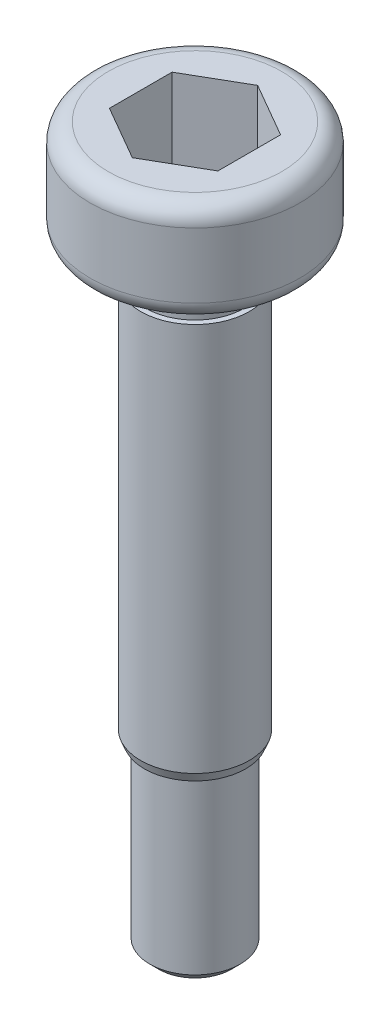
SolidWorks part; units mm, degrees
ref_plane "前视基准面" through (0, 0, 0) normal (0, 0, 1) x (1, 0, 0)
ref_plane "上视基准面" through (0, 0, 0) normal (0, 1, 0) x (1, 0, 0)
ref_plane "右视基准面" through (0, 0, 0) normal (1, 0, 0) x (0, 0, -1)
ref_plane "基准面1" through (0, 0, 0) normal (0, 0, -1) x (-1, 0, 0)
sketch "草图1" plane through (0, 0, 0) normal (0, 0, -1) x (-1, 0, 0)
  line L0 (-1.4, -14.8) -> (0, -14.8)
  line L1 (0, -14.8) -> (0, 0)
  line L2 (0, 0) -> (-2.9, 0)
  line L3 (-2.9, 0) -> (-2.9, -2.8)
  line L4 (-2.9, -2.8) -> (-1.35, -2.8)
  line L5 (-1.35, -2.8) -> (-1.35, -3.8)
  line L6 (-1.35, -3.8) -> (-1.5, -3.8)
  line L7 (-1.5, -3.8) -> (-1.5, -14.55)
  line L8 (-1.5, -14.55) -> (-1.4, -14.8)
  line L9 (0, -14.8) -> (0, 0) construction
  point P9 (1.4608, 0.8002)
  dimension "D1" = 0.25
  dimension "D2" = 0.1
  dimension "D3" = 0.15
  dimension "D4" = 1
  dimension "D5" = 2.8
  dimension "D6" = 2.9
  dimension "D7" = 1.5
  dimension "D8" = 12
revolve "旋转1" add sketch "草图1" angle 360 about L9
sketch "草图2" plane through (0, -14.8, 0) normal (0, -1, 0) x (1, 0, 0)
  circle A0 centre (0, 0) radius 1.25
  dimension "D1" = 2.5
extrude "凸台-拉伸1" add sketch "草图2" along normal blind 4.75
cosmetic thread "装饰螺纹线1" parameters "D2"=2.439
sketch "草图3" plane through (0, -19.55, 0) normal (0, -1, 0) x (1, 0, 0)
  circle A0 centre (0, 0) radius 1.25
  dimension "D1" = 2.5
extrude "凸台-拉伸2" add sketch "草图3" along normal blind 0.25 draft 45
sketch "草图4" plane through (0, 0, 0) normal (0, 1, 0) x (-1, 0, 0)
  line L0 (-1.5, 0.866) -> (-1.5, -0.866)
  line L1 (-1.5, -0.866) -> (0, -1.7321)
  line L2 (0, -1.7321) -> (1.5, -0.866)
  line L3 (1.5, -0.866) -> (1.5, 0.866)
  line L4 (1.5, 0.866) -> (0, 1.7321)
  line L5 (0, 1.7321) -> (-1.5, 0.866)
extrude "切除-拉伸1" cut sketch "草图4" against normal blind 2.4
fillet "圆角1" radius 0.5 2 edges at (0, 0, 2.9) (0, -2.8, 2.9)
